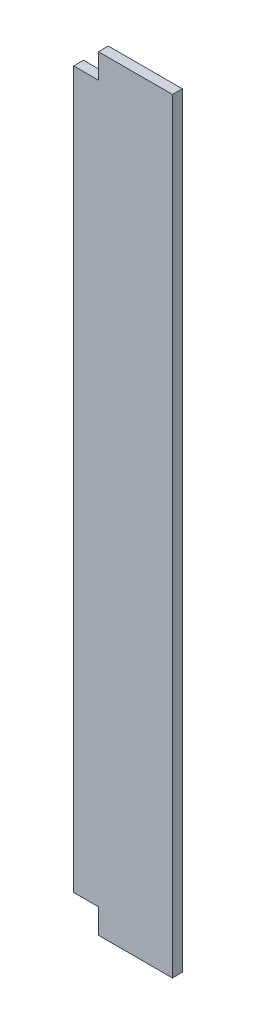
SolidWorks part; units mm, degrees
ref_plane "Plano frontal" through (0, 0, 0) normal (0, 0, 1) x (1, 0, 0)
ref_plane "Plano superior" through (0, 0, 0) normal (0, 1, 0) x (1, 0, 0)
ref_plane "Plano direito" through (0, 0, 0) normal (1, 0, 0) x (0, 0, -1)
sketch "Esboço1" plane through (0, 0, 0) normal (0, 1, 0) x (1, 0, 0)
  line L1 (-129.6089, 67.4581) -> (70.3911, 67.4581)
  line L2 (-129.6089, 67.4581) -> (-129.6089, 47.4581)
  line L3 (-129.6089, 47.4581) -> (70.3911, 47.4581)
  line L4 (70.3911, 67.4581) -> (70.3911, 47.4581)
  dimension "D1" = 200
  dimension "D2" = 20
extrude "Ressalto-extrusão1" add sketch "Esboço1" along normal blind 1550
sketch "Esboço2" plane through (0, 0, -47.4581) normal (0, 0, 1) x (1, 0, 0)
  line L0 (-129.6089, 1550) -> (-129.6089, 0) construction
  line L1 (-79.6089, 0) -> (-129.6089, 0)
  line L2 (-79.6089, 0) -> (-79.6089, 50)
  line L3 (-79.6089, 50) -> (-129.6089, 50)
  line L4 (-129.6089, 0) -> (-129.6089, 50)
  dimension "D1" = 50
  dimension "D2" = 50
extrude "Corte-extrusão1" cut sketch "Esboço2" against normal through all
sketch "Esboço3" plane through (0, 0, -47.4581) normal (0, 0, 1) x (1, 0, 0)
  line L0 (-129.6089, 1550) -> (-129.6089, 50) construction
  line L1 (-79.6089, 1550) -> (-129.6089, 1550)
  line L2 (-79.6089, 1550) -> (-79.6089, 1500)
  line L3 (-79.6089, 1500) -> (-129.6089, 1500)
  line L4 (-129.6089, 1550) -> (-129.6089, 1500)
  dimension "D1" = 50
  dimension "D2" = 50
extrude "Corte-extrusão2" cut sketch "Esboço3" against normal through all
